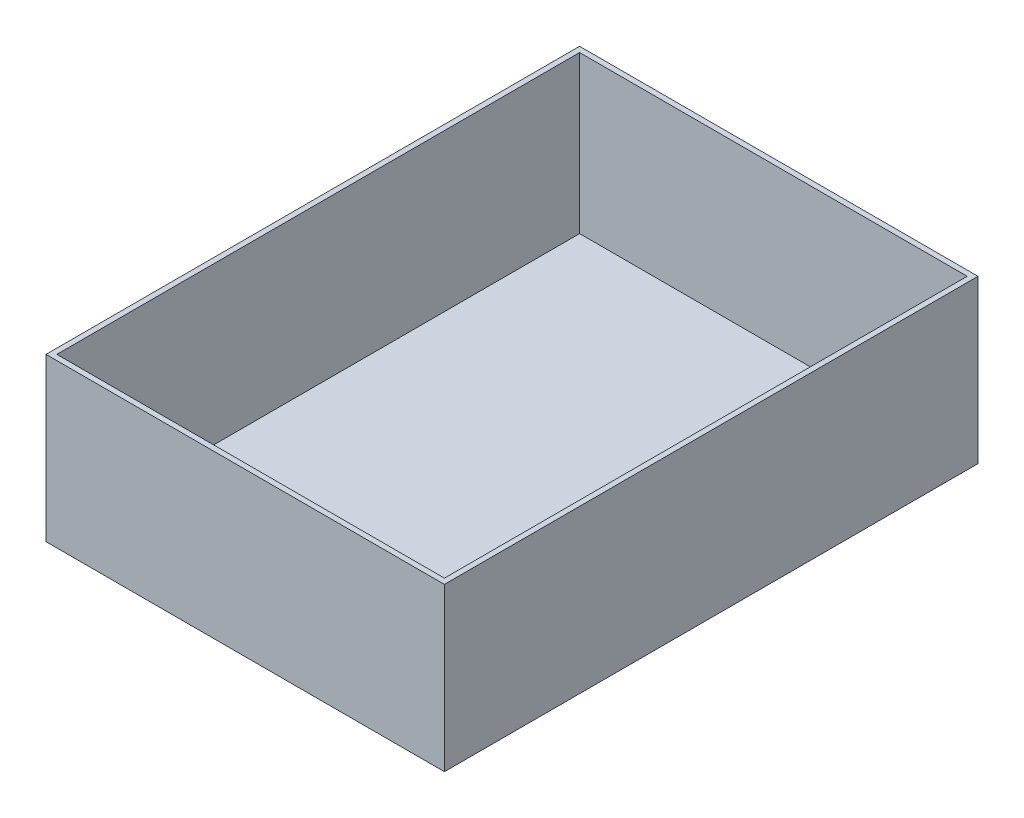
SolidWorks part; units mm, degrees
material "Luft"
ref_plane "Ebene vorne" through (0, 0, 0) normal (0, 0, 1) x (1, 0, 0)
ref_plane "Ebene oben" through (0, 0, 0) normal (0, 1, 0) x (1, 0, 0)
ref_plane "Ebene rechts" through (0, 0, 0) normal (1, 0, 0) x (0, 0, -1)
sketch "Skizze1" plane through (0, 0, 0) normal (0, 0, 1) x (1, 0, 0)
  line L1 (-107.5, -43.5) -> (107.5, -43.5)
  line L2 (-107.5, -43.5) -> (-107.5, 43.5)
  line L3 (-107.5, 43.5) -> (107.5, 43.5)
  line L4 (107.5, -43.5) -> (107.5, 43.5)
  line L5 (-107.5, -43.5) -> (107.5, 43.5) construction
  line L6 (-107.5, 43.5) -> (107.5, -43.5) construction
  point P0 (0, 0)
  dimension "D1" = 215
  dimension "D2" = 87
extrude "Aufsatz-Linear austragen1" add sketch "Skizze1" along normal mid plane 290
shell "Wandung1" thickness 3
